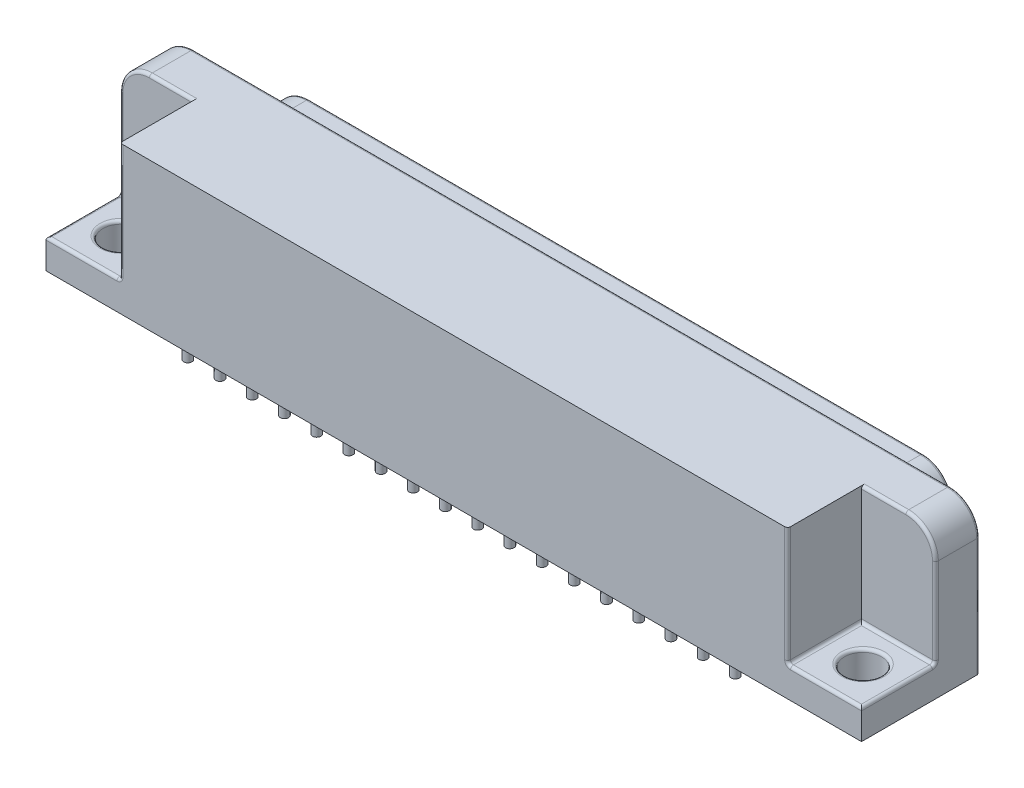
SolidWorks part; units mm, degrees
ref_plane "x/y" through (0, 0, 0) normal (0, 0, 1) x (1, 0, 0)
ref_plane "x/z" through (0, 0, 0) normal (0, 1, 0) x (1, 0, 0)
ref_plane "y/z" through (0, 0, 0) normal (1, 0, 0) x (0, 0, -1)
sketch "Sketch1" plane through (0, 0, 0) normal (0, 1, 0) x (1, 0, 0)
  line L1 (-10.16, -2.032) -> (59.944, -2.032)
  line L2 (-10.16, -2.032) -> (-10.16, 8.128)
  line L3 (-10.16, 8.128) -> (59.944, 8.128)
  line L4 (59.944, -2.032) -> (59.944, 8.128)
  point P3 (24.892, 8.128)
  dimension "D1" = 70.104
  dimension "D2" = 10.16
  dimension "D3" = 2.032
  dimension "D4" = 10.16
extrude "Base-Extrude" add sketch "Sketch1" along normal blind 12.7
sketch "Sketch2" plane through (0, 0, -8.128) normal (0, 0, -1) x (-1, 0, 0)
  line L0 (-24.892, 12.7) -> (-24.892, -6.5379) construction
  line L1 (-59.944, 12.7) -> (10.16, 12.7) construction
  line L2 (-50.7446, 2.286) -> (0.9606, 2.286)
  line L3 (3.4543, 4.3435) -> (3.9949, 7.1375)
  line L4 (1.5011, 10.16) -> (-51.2851, 10.16)
  line L6 (-53.2383, 4.3435) -> (-53.7789, 7.1375)
  line L7 (-59.944, 0) -> (10.16, 0) construction
  arc A0 (3.4543, 4.3435) -> (0.9606, 2.286) centre (0.9606, 4.826) cw
  arc A1 (1.5011, 10.16) -> (3.9949, 7.1375) centre (1.5011, 7.62) cw
  arc A2 (-51.2851, 10.16) -> (-53.7789, 7.1375) centre (-51.2851, 7.62) ccw
  arc A3 (-53.2383, 4.3435) -> (-50.7446, 2.286) centre (-50.7446, 4.826) ccw
  point P4 (-24.892, 10.16)
  point P12 (3.0563, 2.286)
  point P21 (-24.892, 2.286)
  dimension "D5" = 2.54
  dimension "D1" = 2.286
  dimension "D2" = 2.54
  dimension "D3" = 100.95
  dimension "D4" = 27.9483
extrude "Boss-Extrude1" add sketch "Sketch2" along normal blind 3.81
sketch "Sketch4" plane through (0, 0, -11.938) normal (0, 0, -1) x (-1, 0, 0)
  line L0 (10.16, 12.7) -> (10.16, 0) construction
  line L2 (-59.944, 12.7) -> (10.16, 12.7) construction
  circle A0 centre (0, 7.62) radius 0.635
  dimension "D1" = 1.27
  dimension "D2" = 10.16
  dimension "D3" = 5.08
extrude "Cut-Extrude1" cut sketch "Sketch4" against normal blind 5.08
sketch "Sketch5" plane through (0, 0, -11.938) normal (0, 0, -1) x (-1, 0, 0)
  line L0 (10.16, 12.7) -> (10.16, 0) construction
  line L2 (-59.944, 0) -> (10.16, 0) construction
  circle A0 centre (-1.397, 5.08) radius 0.635
  circle A1 centre (0, 7.62) radius 0.635 construction
  dimension "D2" = 5.08
  dimension "D1" = 11.557
extrude "Cut-Extrude2" cut sketch "Sketch5" against normal blind 5.08
sketch "Sketch6" plane through (0, 0, 0) normal (0, -1, 0) x (1, 0, 0)
  circle A0 centre (0, 0) radius 0.3556
  dimension "D1" = 0.7112
extrude "Boss-Extrude2" add sketch "Sketch6" along normal blind 2.54
pattern_linear "LPattern1" count 19 spacing 2.7686 along (1, 0, 0) skipping (18, 0) of "Boss-Extrude2"
pattern_linear "LPattern2" count 19 spacing 2.7686 along (1, 0, 0) of "Cut-Extrude1"
pattern_linear "LPattern3" count 18 spacing 2.7686 along (1, 0, 0) of "Cut-Extrude2"
sketch "Sketch7" plane through (0, 0, 0) normal (0, -1, 0) x (1, 0, 0)
  line L1 (-10.16, -8.128) -> (-10.16, 2.032) construction
  circle A0 centre (1.397, -2.54) radius 0.3556
  dimension "D1" = 0.7112
  dimension "D2" = 11.557
  dimension "D3" = 2.54
extrude "Boss-Extrude3" add sketch "Sketch7" along normal up to surface (2.54 mm away) up to face at (0, -2.54, -0.3556)
pattern_linear "LPattern4" count 17 spacing 2.7686 along (1, 0, 0) of "Boss-Extrude3"
ref_plane "Plane1" through (24.892, 0, 0) normal (1, 0, 0) x (0, 0, -1)
sketch "Sketch9" plane through (0, 0, 2.032) normal (0, 0, 1) x (1, 0, 0)
  line L1 (-10.16, 12.7) -> (-3.8049, 12.7)
  line L2 (-10.16, 12.7) -> (-10.16, 2.54)
  line L3 (-10.16, 2.54) -> (-3.8049, 2.54)
  line L4 (-3.8049, 12.7) -> (-3.8049, 2.54)
  dimension "D1" = 10.16
  dimension "D2" = 6.3551
extrude "Cut-Extrude3" cut sketch "Sketch9" against normal blind 6.35
sketch "Sketch11" plane through (0, 2.54, 0) normal (0, 1, 0) x (-1, 0, 0)
  line L0 (10.16, 2.032) -> (3.8049, 2.032) construction
  line L1 (10.16, -4.318) -> (10.16, 2.032) construction
  circle A0 centre (6.985, -1.27) radius 1.5875
  point P2 (6.9825, 2.032)
  dimension "D1" = 3.175
  dimension "D2" = 3.302
  dimension "D3" = 3.175
extrude "Cut-Extrude4" cut sketch "Sketch11" against normal through all
mirror "Mirror1" about plane through (24.892, 0, 0) normal (1, 0, 0) of "Cut-Extrude4", "Cut-Extrude3"
fillet "Fillet1" radius 2.54 2 edges at (-10.16, 12.7, -6.223) (59.944, 7.62, -4.318)
fillet "Fillet2" radius 0.254 68 edges at (7.6708, 7.62, -11.938) (10.4394, 7.62, -11.938) (13.208, 7.62, -11.938) (15.9766, 7.62, -11.938) (18.7452, 7.62, -11.938) (21.5138, 7.62, -11.938) (24.2824, 7.62, -11.938) (27.051, 7.62, -11.938) (29.8196, 7.62, -11.938) (32.5882, 7.62, -11.938) (35.3568, 7.62, -11.938) (38.1254, 7.62, -11.938) (40.894, 7.62, -11.938) (43.6626, 7.62, -11.938) (46.4312, 7.62, -11.938) (49.1998, 7.62, -11.938) (3.5306, 5.08, -11.938) (6.2992, 5.08, -11.938) (9.0678, 5.08, -11.938) (11.8364, 5.08, -11.938) (14.605, 5.08, -11.938) (17.3736, 5.08, -11.938) (20.1422, 5.08, -11.938) (22.9108, 5.08, -11.938) (25.6794, 5.08, -11.938) (28.448, 5.08, -11.938) (31.2166, 5.08, -11.938) (33.9852, 5.08, -11.938) (36.7538, 5.08, -11.938) (39.5224, 5.08, -11.938) (-2.5771, 2.8668, -11.938) (42.291, 5.08, -11.938) (-3.7246, 5.7405, -11.938) (45.0596, 5.08, -11.938) (-3.4604, 9.2365, -11.938) (47.8282, 5.08, -11.938) (24.892, 10.16, -11.938) (53.2444, 9.2365, -11.938) (53.5086, 5.7405, -11.938) (52.3611, 2.8668, -11.938) (24.892, 2.286, -11.938) (-10.16, 2.54, -1.143) (-5.7125, 12.7, -4.318) (-6.9825, 2.54, -4.318) (-3.8049, 2.54, -1.143) (-6.9825, 2.54, 2.032) (-3.8049, 7.62, 2.032) (-6.985, 2.54, 0.3175) (56.7665, 2.54, 2.032) (59.944, 2.54, -1.143) (53.5889, 7.62, 2.032) (53.5889, 2.54, -1.143) (56.7665, 2.54, -4.318) (55.4965, 12.7, -4.318) (56.769, 2.54, 0.3175) (24.892, 12.7, -8.128) (-10.16, 6.35, -4.318) (-9.4161, 11.9561, -4.318) (-10.16, 5.08, -8.128) (59.944, 5.08, -8.128) (59.2001, 11.9561, -8.128) (-9.4161, 11.9561, -8.128) (59.944, 6.35, -4.318) (59.2001, 11.9561, -4.318) (-0.635, 7.62, -11.938) (0.762, 5.08, -11.938) (2.1336, 7.62, -11.938) (4.9022, 7.62, -11.938)
